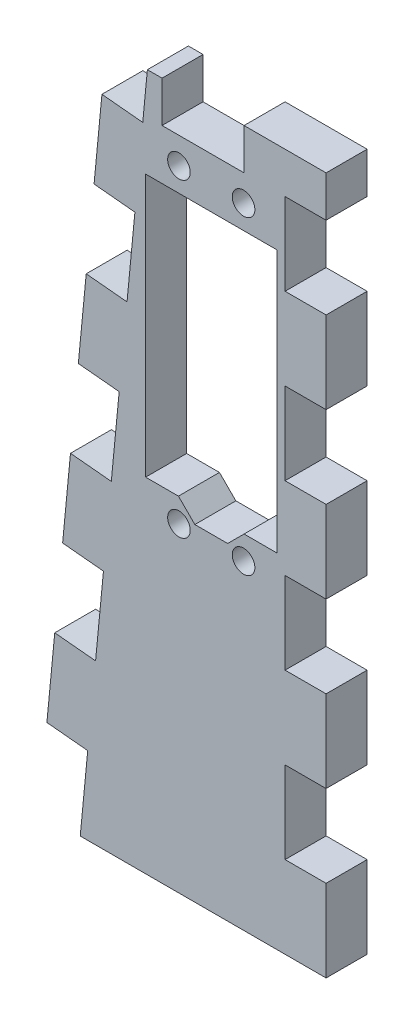
SolidWorks part; units mm, degrees
ref_plane "Front Plane" through (0, 0, 0) normal (0, 0, 1) x (1, 0, 0)
ref_plane "Top Plane" through (0, 0, 0) normal (0, 1, 0) x (1, 0, 0)
ref_plane "Right Plane" through (0, 0, 0) normal (1, 0, 0) x (0, 0, -1)
sketch "Sketch1" plane through (0, 0, 0) normal (0, 0, 1) x (1, 0, 0)
  line L0 (0, 0) -> (40.3547, 419.1) construction
  line L1 (40.3547, 419.1) -> (159.2585, 419.1) construction
  line L2 (159.2585, 419.1) -> (159.2585, 0) construction
  line L3 (159.2585, 0) -> (0, 0) construction
  line L4 (159.2585, -1000) -> (159.2585, 49000) construction
  line L5 (2.0164, 20.9415) -> (40.3547, 419.1) construction
  line L6 (2.0164, 20.9415) -> (41.8323, 17.1077) construction
  line L7 (40.3547, 419.1) -> (80.1706, 415.2662) construction
  line L8 (41.8323, 17.1077) -> (80.1706, 415.2662) construction
  line L9 (64.0085, -1000) -> (64.0085, 49000) construction
  line L10 (-42.7214, 317.5) -> (-118.5706, 324.8034) construction
  line L11 (-20.0013, 414.3375) -> (40.196, 414.3375) construction
  line L12 (-1162.1335, 304.8) -> (48837.8665, 304.8) construction
  line L13 (-120.1415, 292.1) -> (-43.9415, 292.1) construction
  line L14 (-118.5706, 324.8034) -> (-43.9415, 292.1) construction
  line L15 (-42.7214, 317.5) -> (-120.1415, 292.1) construction
  line L16 (40.196, 338.1375) -> (-20.0013, 338.1375) construction
  line L17 (-128.0517, 325.7164) -> (29.8985, 310.5075)
  line L18 (-128.0517, 325.7164) -> (-127.4431, 332.0371)
  line L19 (-127.4431, 332.0371) -> (40.3547, 419.1)
  line L20 (40.3547, 419.1) -> (100.3991, 419.1)
  line L21 (108.4585, 419.1) -> (108.4585, 0) construction
  line L22 (29.8985, 310.5075) -> (0.4102, 4.2603)
  line L23 (0.4102, 4.2603) -> (44.6556, 0)
  line L24 (44.6556, 0) -> (108.4585, 0)
  line L25 (111.8902, 411.8076) -> (159.2585, 311.15)
  line L26 (159.2585, 311.15) -> (159.2585, 304.8)
  line L27 (159.2585, 304.8) -> (108.4585, 280.8941)
  line L28 (108.4585, 280.8941) -> (108.4585, 0)
  line L29 (100.3991, 406.4) -> (28627.168, -40334.0482) construction
  line L30 (107.4945, 405.1489) -> (48105.9225, -8058.269) construction
  line L31 (46.2285, 266.7) -> (77.1396, 255.4859) construction
  line L32 (46.2285, 266.7) -> (77.1396, 277.9141) construction
  line L33 (114.9679, 385.5935) -> (125.3711, 392.878) construction
  line L34 (125.4132, 401.9893) -> (127.6185, 414.4964) construction
  line L35 (77.1396, 277.9141) -> (127.6185, 414.4964) construction
  line L36 (125.3711, 392.878) -> (77.1396, 255.4859) construction
  line L37 (77.1396, 277.9141) -> (64.0085, 277.9141) construction
  line L38 (77.1396, 255.4859) -> (64.0085, 255.4859) construction
  arc A0 (-118.5706, 324.8034) -> (-20.0013, 414.3375) centre (-20.0013, 315.3123) cw construction
  arc A1 (73.5335, 304.8) -> (40.196, 338.1375) centre (40.196, 304.8) ccw construction
  arc A2 (149.7335, 304.8) -> (40.196, 414.3375) centre (40.196, 304.8) ccw construction
  arc A3 (-42.7214, 317.5) -> (-20.0013, 338.1375) centre (-20.0013, 315.3123) cw construction
  arc A4 (100.3991, 419.1) -> (111.8902, 411.8076) centre (100.3991, 406.4) cw
  point P7 (57.6585, 400.05)
  point P17 (149.7335, 304.8)
  point P18 (73.5335, 304.8)
  dimension "D9" = 9.525
  dimension "D14" = 25.4
  dimension "D22" = 12.7
  dimension "D1" = 419.1
  dimension "D2" = 101.6
  dimension "D3" = 19.05
  dimension "D4" = 19.05
  dimension "D5" = 84.5
  dimension "D6" = 40
  dimension "D7" = 400
  dimension "D8" = 95.25
  dimension "D10" = 9.525
  dimension "D11" = 114.3
  dimension "D12" = 76.2
  dimension "D13" = 9.525
  dimension "D15" = 127
  dimension "D16" = 9.525
  dimension "D17" = 203.2
  dimension "D18" = 6.35
  dimension "D19" = 50.8
  dimension "D20" = 44.45
  dimension "D21" = 6.35
  dimension "D23" = 55
  dimension "D24" = 25.4
  dimension "D25" = 12.7
  dimension "D26" = 25.4
  dimension "D27" = 12.7
  dimension "D28" = 17.78
  dimension "D29" = 38.1
  dimension "D30" = 39.88
  dimension "D31" = 10
sketch "Sketch2" plane through (0, 0, 0) normal (0, 0, 1) x (1, 0, 0)
  line L0 (19.5659, 203.2) -> (29.9603, 311.15)
  line L1 (29.8985, 310.5075) -> (0.4102, 4.2603) construction
  line L2 (29.9603, 311.15) -> (64.0085, 311.15)
  line L3 (64.0085, -201000) -> (64.0085, 249000) construction
  line L4 (64.0085, 311.15) -> (64.0085, 203.2)
  line L5 (64.0085, 203.2) -> (19.5659, 203.2)
  line L6 (0, 0) -> (40.3547, 419.1) construction
  line L7 (-201162.1335, 304.8) -> (248837.8665, 304.8) construction
  dimension "D1" = 101.6
extrude "Boss-Extrude1" add sketch "Sketch2" along normal blind 6.35
sketch "Sketch4" plane through (0, 0, 6.35) normal (0, 0, 1) x (1, 0, 0)
  line L0 (56.3885, 256.38) -> (56.3885, 297.02)
  line L1 (56.3885, 256.38) -> (36.0685, 256.38) construction
  line L2 (56.3885, 297.02) -> (36.0685, 297.02)
  line L3 (36.0685, 256.38) -> (36.0685, 297.02)
  line L4 (56.3885, 256.38) -> (36.0685, 297.02) construction
  line L5 (56.3885, 297.02) -> (36.0685, 256.38) construction
  line L6 (64.0085, 311.15) -> (29.9603, 311.15) construction
  line L7 (51.2285, 252.7) -> (51.2285, 300.7) construction
  line L8 (51.2285, 252.7) -> (41.2285, 252.7) construction
  line L9 (51.2285, 300.7) -> (41.2285, 300.7) construction
  line L10 (41.2285, 252.7) -> (41.2285, 300.7) construction
  line L11 (51.2285, 252.7) -> (41.2285, 300.7) construction
  line L12 (51.2285, 300.7) -> (41.2285, 252.7) construction
  line L13 (36.0685, 256.38) -> (41.1485, 256.38)
  line L14 (41.1485, 256.38) -> (43.6885, 253.84)
  line L15 (43.6885, 253.84) -> (48.7685, 253.84)
  line L16 (48.7685, 253.84) -> (51.3085, 256.38)
  line L17 (51.3085, 256.38) -> (56.3885, 256.38)
  line L18 (46.2285, 253.84) -> (46.2285, 276.7) construction
  line L43 (64.0085, -201000) -> (64.0085, 249000) construction
  line L44 (36.0685, 297.02) -> (56.3885, 297.02) construction
  line L45 (36.0685, 297.02) -> (36.0685, 303.62) construction
  line L46 (57.6585, 209.55) -> (57.6585, 304.8)
  line L47 (26.5567, 209.55) -> (57.6585, 209.55)
  line L48 (57.6585, 304.8) -> (35.7283, 304.8)
  line L49 (35.7283, 304.8) -> (26.5567, 209.55)
  line L50 (57.6585, 209.55) -> (57.6585, 304.8) construction
  line L51 (26.5567, 209.55) -> (57.6585, 209.55) construction
  line L52 (57.6585, 304.8) -> (35.7283, 304.8) construction
  line L53 (35.7283, 304.8) -> (26.5567, 209.55) construction
  line L54 (36.0685, 303.62) -> (56.3885, 303.62) construction
  line L55 (56.3885, 297.02) -> (56.3885, 303.62) construction
  line L56 (-201162.1335, 304.8) -> (248837.8665, 304.8) construction
  circle A0 centre (41.2285, 300.7) radius 1.75
  circle A1 centre (51.2285, 300.7) radius 1.75
  circle A2 centre (41.2285, 252.7) radius 1.75
  circle A3 centre (51.2285, 252.7) radius 1.75
  point P1 (46.2285, 276.7)
  point P8 (46.2285, 266.7)
  point P9 (46.2285, 276.7)
  dimension "D3" = 3.5
  dimension "D10" = 6.35
  dimension "D1" = 40.64
  dimension "D2" = 20.32
  dimension "D4" = 10
  dimension "D5" = 48
  dimension "D6" = 5.08
  dimension "D7" = 2.54
  dimension "D8" = 135
  dimension "D9" = 14
  dimension "D11" = 6.6
  dimension "D12" = 17.78
  dimension "D13" = 38.1
extrude "Cut-Extrude1" cut sketch "Sketch4" against normal through all
sketch "Sketch6" plane through (0, 0, 6.35) normal (0, 0, 1) x (1, 0, 0)
  line L0 (64.0085, 203.2) -> (64.0085, 311.15) construction
  line L1 (64.0085, 304.8) -> (57.6585, 304.8)
  line L2 (64.0085, 304.8) -> (64.0085, 292.1)
  line L3 (64.0085, 292.1) -> (57.6585, 292.1)
  line L4 (57.6585, 304.8) -> (57.6585, 292.1)
  dimension "D1" = 6.35
  dimension "D2" = 12.7
  dimension "D3" = 6.35
extrude "Cut-Extrude2" cut sketch "Sketch6" against normal through all
pattern_linear "LPattern1" count 5 spacing 25.4 along (0, -1, 0) of "Cut-Extrude2"
sketch "Sketch7" plane through (0, 0, 6.35) normal (0, 0, 1) x (1, 0, 0)
  line L0 (64.0085, 311.15) -> (29.9603, 311.15) construction
  line L1 (38.6085, 311.15) -> (51.3085, 311.15)
  line L2 (38.6085, 311.15) -> (38.6085, 304.8)
  line L3 (38.6085, 304.8) -> (51.3085, 304.8)
  line L4 (51.3085, 311.15) -> (51.3085, 304.8)
  line L5 (64.0085, 304.8) -> (64.0085, 311.15) construction
  dimension "D1" = 12.7
  dimension "D2" = 12.7
  dimension "D3" = 6.35
extrude "Cut-Extrude3" cut sketch "Sketch7" against normal through all
sketch "Sketch8" plane through (0, 0, 6.35) normal (0, 0, 1) x (1, 0, 0)
  line L0 (19.5659, 203.2) -> (20.7832, 215.8415)
  line L1 (19.5659, 203.2) -> (25.8867, 202.5914)
  line L2 (20.7832, 215.8415) -> (27.1039, 215.2329)
  line L3 (25.8867, 202.5914) -> (27.1039, 215.2329)
  line L4 (29.9603, 311.15) -> (19.5659, 203.2) construction
  dimension "D1" = 12.7
  dimension "D2" = 6.35
extrude "Cut-Extrude4" cut sketch "Sketch8" against normal through all
pattern_linear "LPattern2" count 5 spacing 25.4 along (0.0958, 0.9954, 0) of "Cut-Extrude4"
